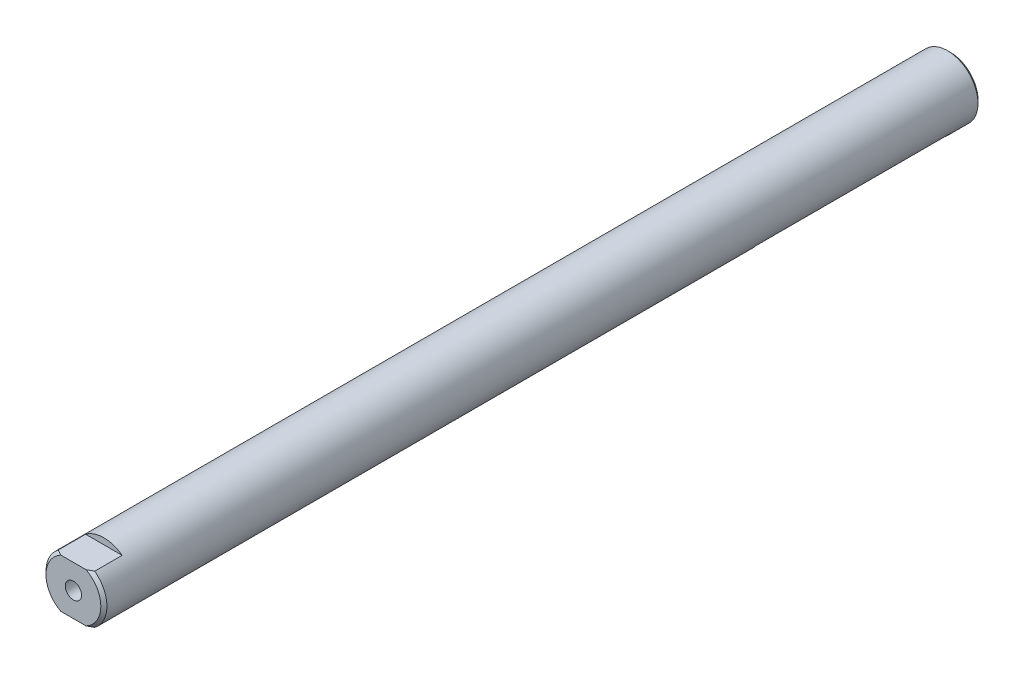
SolidWorks part; units mm, degrees
material "6061-T6 (SS)"
ref_plane "Front Plane" through (0, 0, 0) normal (0, 0, 1) x (1, 0, 0)
ref_plane "Top Plane" through (0, 0, 0) normal (0, 1, 0) x (1, 0, 0)
ref_plane "Right Plane" through (0, 0, 0) normal (1, 0, 0) x (0, 0, -1)
sketch "Sketch1" plane through (0, 0, 0) normal (0, 0, 1) x (1, 0, 0)
  circle A0 centre (0, 0) radius 15.875
  dimension "D1" = 31.75
extrude "Boss-Extrude1" add sketch "Sketch1" along normal mid plane 457.2
ref_plane "Plane1" through (0, -19.05, 0) normal (0, 1, 0) x (1, 0, 0)
sketch "Sketch2" plane through (0, -19.05, 0) normal (0, 1, 0) x (1, 0, 0)
  line L0 (15.875, 228.6) -> (-15.875, 228.6) construction
  line L1 (-25.4, 216.154) -> (25.4, 216.154)
  line L2 (-25.4, 216.154) -> (-25.4, 114.173)
  line L3 (-25.4, 114.173) -> (25.4, 114.173)
  line L4 (25.4, 216.154) -> (25.4, 114.173)
  point P6 (0, 216.154)
  dimension "D1" = 12.446
  dimension "D2" = 101.981
  dimension "D3" = 50.8
extrude "Cut-Extrude2" cut sketch "Sketch2" along normal blind 9.525
chamfer "Chamfer1" distance 1.5875 angle 45 2 edges at (15.875, 0, 228.6) (15.875, 0, -228.6)
sketch "Sketch3" plane through (0, 0, 228.6) normal (0, 0, 1) x (1, 0, 0)
  line L1 (-9.525, 22.7486) -> (9.525, 22.7486)
  line L2 (-9.525, 22.7486) -> (-9.525, 12.7)
  line L3 (-9.525, 12.7) -> (9.525, 12.7)
  line L4 (9.525, 22.7486) -> (9.525, 12.7)
  line L5 (-9.525, -21.2823) -> (9.525, -21.2823)
  line L6 (-9.525, -21.2823) -> (-9.525, -12.7)
  line L7 (-9.525, -12.7) -> (9.525, -12.7)
  line L8 (9.525, -21.2823) -> (9.525, -12.7)
  circle A0 centre (0, 0) radius 15.875 construction
  point P11 (0, -12.7)
  point P13 (0, 12.7)
  dimension "D1" = 25.4
extrude "Cut-Extrude3" cut sketch "Sketch3" against normal blind 15.875
hole_wizard "M10x1.5 Tapped Hole1" positions "Sketch4" profile "Sketch5" tap size "M10x1.5" standard "ANSI Metric"
sketch "Sketch4" plane through (0, 0, 228.6) normal (0, 0, 1) x (1, 0, 0)
  point P0 (0, 0)
sketch "Sketch5" plane through (0, 0, 228.6) normal (1, 0, 0) x (0, -1, 0)
  line L0 (0, 0) -> (0, 30.2397)
  line L1 (0, 30.2397) -> (4.25, 27.686)
  line L2 (4.25, 27.686) -> (4.25, 0)
  line L5 (4.25, 0) -> (0, 0)
  line L10 (0, 30.2397) -> (-4.25, 27.686) construction
  line L11 (0, -6.35) -> (0, 107.95) construction
  dimension "Tap Drill Dia." = 8.5
  dimension "Tap Drill Depth" = 27.686
  dimension "Drill Angle" = 118
cosmetic thread "Hole Thread1" parameters "D1"=20.066, "D2"=10
